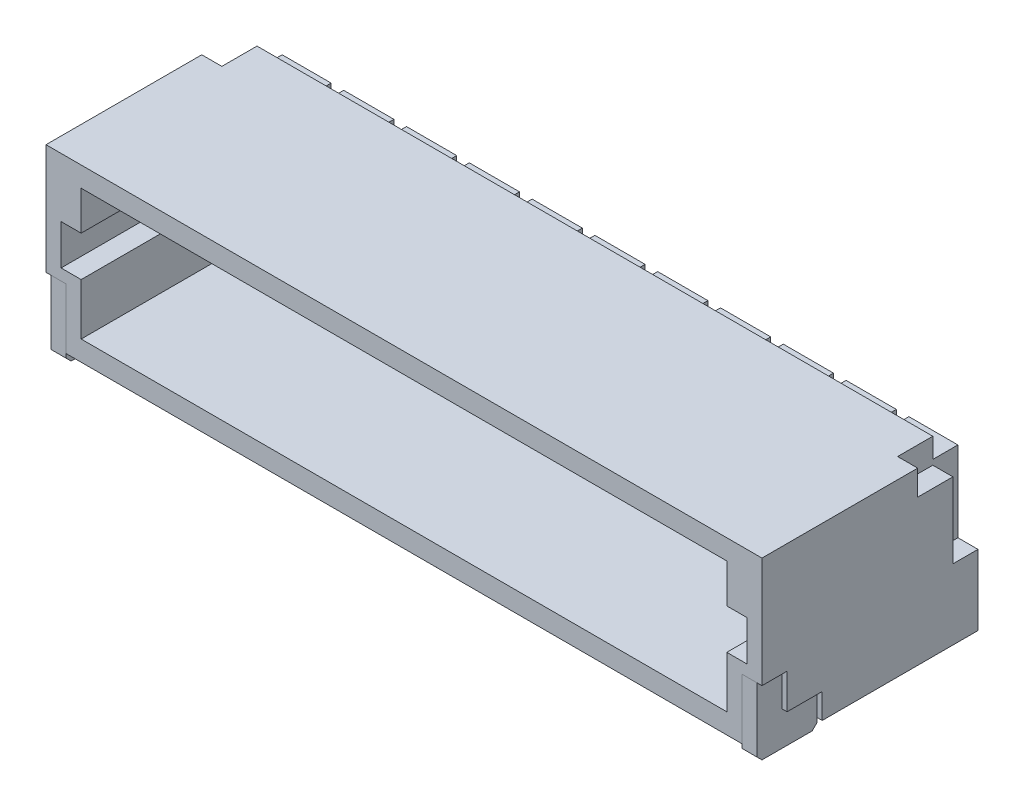
SolidWorks part; units mm, degrees
ref_plane "Front" through (0, 0, 0) normal (0, 0, 1) x (1, 0, 0)
ref_plane "Top" through (0, 0, 0) normal (0, 1, 0) x (1, 0, 0)
ref_plane "Right" through (0, 0, 0) normal (1, 0, 0) x (0, 0, -1)
sketch "Sketch1" plane through (0, 0, 0) normal (0, 0, 1) x (1, 0, 0)
  line L1 (4, -1.7) -> (-4, -1.7)
  line L2 (4, -1.7) -> (4, 1.7)
  line L3 (4, 1.7) -> (-4, 1.7)
  line L4 (-4, -1.7) -> (-4, 1.7)
  line L5 (4, -1.7) -> (-4, 1.7) construction
  line L6 (4, 1.7) -> (-4, -1.7) construction
  point P0 (0, 0)
  dimension "D1" = 3.4
  dimension "D2" = 8
extrude "Boss-Extrude1" add sketch "Sketch1" along normal mid plane 4.3
sketch "Sketch2" plane through (0, 0, 2.15) normal (0, 0, 1) x (1, 0, 0)
  line L0 (4, 1.7) -> (-4, 1.7) construction
  line L1 (3.3, -1.3) -> (-3.3, -1.3)
  line L2 (3.3, -1.3) -> (3.3, -0.275)
  line L3 (3.3, 1.3) -> (-3.3, 1.3)
  line L4 (-3.3, -1.3) -> (-3.3, -0.275)
  line L5 (3.3, -1.3) -> (-3.3, 1.3) construction
  line L6 (3.3, 1.3) -> (-3.3, -1.3) construction
  line L7 (-4, 1.7) -> (-4, -1.7) construction
  line L8 (-3.3, 0.525) -> (-3.3, 1.3)
  line L9 (-3.3, 0.525) -> (-3.7, 0.525)
  line L10 (-3.3, 0.525) -> (-3.3, -0.275) construction
  line L11 (-3.3, -0.275) -> (-3.7, -0.275)
  line L12 (-3.7, 0.525) -> (-3.7, -0.275)
  line L13 (3.3, 0.525) -> (3.7, 0.525)
  line L14 (3.3, 0.525) -> (3.3, -0.275) construction
  line L15 (3.3, -0.275) -> (3.7, -0.275)
  line L16 (3.7, 0.525) -> (3.7, -0.275)
  line L17 (-3.3, -0.275) -> (-3.3, 0.525) construction
  line L18 (3.3, 0.525) -> (3.3, 1.3)
  line L19 (3.3, -0.275) -> (3.3, 0.525) construction
  point P0 (0, 0)
  dimension "D1" = 0.4
  dimension "D2" = 0.7
  dimension "D3" = 0.4
  dimension "D4" = 0.8
  dimension "D5" = 1.175
extrude "Cut-Extrude1" cut sketch "Sketch2" against normal blind 3
sketch "Sketch5" plane through (-4, 0, 0) normal (-1, 0, 0) x (0, 0, 1)
  line L0 (2.15, -1.7) -> (2.15, -0.5)
  line L1 (2.15, 1.7) -> (2.15, -1.7) construction
  line L2 (2.15, -0.5) -> (1.65, -0.5)
  line L3 (1.65, -0.5) -> (1.65, -1.2)
  line L4 (1.65, -1.2) -> (0.95, -1.2)
  line L5 (0.95, -1.2) -> (0.95, -1.7)
  line L6 (2.15, -1.7) -> (-2.15, -1.7) construction
  line L7 (0.95, -1.7) -> (2.15, -1.7)
  line L14 (-1.65, 1.2) -> (-0.95, 1.2)
  line L15 (-0.95, 1.2) -> (-0.95, 1.7)
  line L16 (-0.95, 1.7) -> (-2.15, 1.7)
  line L17 (-2.15, 1.7) -> (-2.15, 0.5)
  line L18 (-2.15, 0.5) -> (-1.65, 0.5)
  line L19 (-1.65, 0.5) -> (-1.65, 1.2)
  line L20 (2.15, 1.7) -> (-2.15, 1.7) construction
  line L21 (-2.15, 1.7) -> (-2.15, -1.7) construction
  point P8 (0, 0)
  dimension "D1" = 1.2
  dimension "D2" = 0.5
  dimension "D3" = 2
extrude "Cut-Extrude2" cut sketch "Sketch5" against normal blind 0.4
mirror "Mirror1" about plane through (0, 0, 0) normal (1, 0, 0) of "Cut-Extrude2"
sketch "Sketch6" plane through (0, 0, -2.15) normal (0, 0, -1) x (-1, 0, 0)
  line L0 (-4, 1.7) -> (-4, -0.3)
  line L1 (-4, -1.7) -> (-4, 0.5) construction
  line L2 (-4, -0.3) -> (-3.6, -0.3)
  line L3 (-3.6, -0.3) -> (-3.6, 1.3)
  line L4 (-3.6, 1.7) -> (-3.6, 0.5) construction
  line L5 (-3.6, 1.3) -> (3.6, 1.3)
  line L6 (3.6, 1.2) -> (3.6, 1.7) construction
  line L7 (3.6, 1.3) -> (3.6, -0.3)
  line L8 (3.6, -0.3) -> (4, -0.3)
  line L9 (4, 0.5) -> (4, -1.7) construction
  line L10 (4, -0.3) -> (4, 1.7)
  line L11 (4, 1.7) -> (-4, 1.7)
  dimension "D1" = 0.4
  dimension "D2" = 2
extrude "Cut-Extrude3" cut sketch "Sketch6" against normal blind 0.5
sketch "Sketch7" plane through (0, 1.3, 0) normal (0, 1, 0) x (1, 0, 0)
  line L0 (3.6, 2.15) -> (-3.6, 2.15) construction
  line L1 (-0.125, 2.15) -> (0.125, 2.15)
  line L2 (-0.125, 2.15) -> (-0.125, 1.85)
  line L3 (-0.125, 1.85) -> (0.125, 1.85)
  line L4 (0.125, 2.15) -> (0.125, 1.85)
  line L5 (-1.125, 2.15) -> (-1.125, 1.85)
  line L6 (-1.375, 1.85) -> (-1.125, 1.85)
  line L7 (-1.375, 2.15) -> (-1.375, 1.85)
  line L8 (-1.375, 2.15) -> (-1.125, 2.15)
  line L9 (-2.375, 2.15) -> (-2.375, 1.85)
  line L10 (-2.625, 1.85) -> (-2.375, 1.85)
  line L11 (-2.625, 2.15) -> (-2.625, 1.85)
  line L12 (-2.625, 2.15) -> (-2.375, 2.15)
  line L13 (0.125, 2.15) -> (0.125, 1.85)
  line L14 (-0.125, 1.85) -> (0.125, 1.85)
  line L15 (-0.125, 2.15) -> (-0.125, 1.85)
  line L16 (-0.125, 2.15) -> (0.125, 2.15)
  line L17 (-1.125, 2.15) -> (-1.125, 1.85)
  line L18 (-1.375, 1.85) -> (-1.125, 1.85)
  line L19 (-1.375, 2.15) -> (-1.375, 1.85)
  line L20 (-1.375, 2.15) -> (-1.125, 2.15)
  line L21 (1.375, 2.15) -> (1.375, 1.85)
  line L22 (1.125, 1.85) -> (1.375, 1.85)
  line L23 (1.125, 2.15) -> (1.125, 1.85)
  line L24 (1.125, 2.15) -> (1.375, 2.15)
  line L25 (0.125, 2.15) -> (0.125, 1.85)
  line L26 (-0.125, 1.85) -> (0.125, 1.85)
  line L27 (-0.125, 2.15) -> (-0.125, 1.85)
  line L28 (-0.125, 2.15) -> (0.125, 2.15)
  line L29 (1.375, 2.15) -> (1.375, 1.85)
  line L30 (1.125, 1.85) -> (1.375, 1.85)
  line L31 (1.125, 2.15) -> (1.125, 1.85)
  line L32 (1.125, 2.15) -> (1.375, 2.15)
  line L33 (2.625, 2.15) -> (2.625, 1.85)
  line L34 (2.375, 1.85) -> (2.625, 1.85)
  line L35 (2.375, 2.15) -> (2.375, 1.85)
  line L36 (2.375, 2.15) -> (2.625, 2.15)
  point P6 (0, 1.85)
  line M7 (3.6, 2.15) -> (-3.6, 2.15)
  dimension "D1" = 0.25
  dimension "D2" = 0.3
  dimension "D5" = 1
  dimension "D3" = 3
  dimension "D4" = 3
extrude "Cut-Extrude4" cut sketch "Sketch7" against normal through all both and the other way through all contours L23 L22 L21 M7 | L7 L6 L5 M7 | L11 L10 L9 M7 | L4 L2 L3 M7 | L35 L34 L33 L36
sketch "Sketch8" plane through (0, 0, -0.85) normal (0, 0, 1) x (1, 0, 0)
  line L0 (0.125, 1.3) -> (-0.125, 1.3) construction
  line L1 (0.125, 1) -> (-0.125, 1)
  line L2 (1.375, 1) -> (1.375, 0.75)
  line L3 (-0.125, 1) -> (0.125, 1)
  line L4 (-0.125, 1) -> (-0.125, 0.75)
  line L5 (-0.125, 0.75) -> (0.125, 0.75)
  line L6 (0.125, 1) -> (0.125, 0.75)
  line L7 (1.125, 0.75) -> (1.375, 0.75)
  line L8 (1.125, 1) -> (1.125, 0.75)
  line L9 (1.375, 1) -> (1.125, 1)
  line L10 (2.625, 1) -> (2.625, 0.75)
  line L11 (2.375, 0.75) -> (2.625, 0.75)
  line L12 (2.375, 1) -> (2.375, 0.75)
  line L13 (2.625, 1) -> (2.375, 1)
  line L14 (0.125, 1) -> (0.125, 0.75)
  line L15 (-0.125, 0.75) -> (0.125, 0.75)
  line L16 (-0.125, 1) -> (-0.125, 0.75)
  line L17 (0.125, 1) -> (-0.125, 1)
  line L18 (1.375, 1) -> (1.375, 0.75)
  line L19 (1.125, 0.75) -> (1.375, 0.75)
  line L20 (1.125, 1) -> (1.125, 0.75)
  line L21 (1.375, 1) -> (1.125, 1)
  line L22 (-1.125, 1) -> (-1.125, 0.75)
  line L23 (-1.375, 0.75) -> (-1.125, 0.75)
  line L24 (-1.375, 1) -> (-1.375, 0.75)
  line L25 (-1.125, 1) -> (-1.375, 1)
  line L26 (0.125, 1) -> (0.125, 0.75)
  line L27 (-0.125, 0.75) -> (0.125, 0.75)
  line L28 (-0.125, 1) -> (-0.125, 0.75)
  line L29 (0.125, 1) -> (-0.125, 1)
  line L30 (-1.125, 1) -> (-1.125, 0.75)
  line L31 (-1.375, 0.75) -> (-1.125, 0.75)
  line L32 (-1.375, 1) -> (-1.375, 0.75)
  line L33 (-1.125, 1) -> (-1.375, 1)
  line L34 (-2.375, 1) -> (-2.375, 0.75)
  line L35 (-2.625, 0.75) -> (-2.375, 0.75)
  line L36 (-2.625, 1) -> (-2.625, 0.75)
  line L37 (-2.375, 1) -> (-2.625, 1)
  line L38 (3.3, 1.3) -> (-3.3, 1.3) construction
  line L39 (0.125, 1.3) -> (-0.125, 1.3) construction
  dimension "D3" = 1
  dimension "D4" = 0.3
  dimension "D5" = 0.25
  dimension "D1" = 3
  dimension "D2" = 3
extrude "Cut-Extrude5" cut sketch "Sketch8" against normal through all both and the other way through all contours L34 L37 L36 L35 | L22 L25 L24 L23 | L2 L9 L8 L7 | L6 L1 L4 L5 | L10 L13 L12 L11
sketch "Sketch9" plane through (0, 0, 0) normal (1, 0, 0) x (0, 0, -1)
  line L0 (1.85, -1.88) -> (2.95, -1.88)
  line L1 (2.95, -1.88) -> (2.95, -1.63)
  line L2 (2.95, -1.63) -> (2.15, -1.63)
  line L3 (2.15, -1.7) -> (2.15, -0.3) construction
  line L4 (2.15, -1.63) -> (2.15, 1)
  line L5 (2.15, 1.3) -> (2.15, -0.3) construction
  line L6 (2.15, 1) -> (-0.45, 1)
  line L7 (-0.45, 1) -> (-0.45, 0.75)
  line L8 (-0.45, 0.75) -> (1.85, 0.75)
  line L9 (1.85, -1.7) -> (1.85, 0.75) construction
  line L10 (1.85, 0.75) -> (1.85, -1.88)
  line L11 (1.85, 0.75) -> (0.85, 0.75) construction
  line L12 (1.85, 1) -> (0.85, 1) construction
  line L13 (-2.15, -0.5) -> (-2.15, 1.7) construction
  line L14 (-0.95, -1.7) -> (2.15, -1.7) construction
  dimension "D1" = 1.7
  dimension "D2" = 0.8
  dimension "D3" = 0.18
extrude "Boss-Extrude2" add sketch "Sketch9" along normal mid plane 0.25 separate body
chamfer "Chamfer2" distance 0.1 angle 45 1 edges at (0, -1.88, -1.85)
pattern_linear "LPattern1" count 3 spacing 1.25 along (1, 0, 0) count 3 spacing 1.25 along (-1, 0, 0) of bodies 108
sketch "Sketch10" plane through (3.6, 0, 0) normal (1, 0, 0) x (0, 0, -1)
  line L0 (-2.15, -0.5) -> (-2.15, -1.88)
  line L1 (-2.15, -1.88) -> (-0.95, -1.88)
  line L2 (-0.95, -1.88) -> (-0.95, -1.2)
  line L3 (-0.95, -1.2) -> (-1.65, -1.2)
  line L4 (-1.65, -0.5) -> (-1.65, -1.2) construction
  line L5 (-1.65, -1.2) -> (-1.65, -0.5)
  line L6 (-1.65, -0.5) -> (-2.15, -0.5)
  line L7 (-1.65, -1.2) -> (-0.95, -1.2) construction
  line L8 (-0.95, -1.2) -> (-0.95, -1.7) construction
  line L10 (-0.95, -1.7) -> (-2.15, -1.7) construction
  dimension "D1" = 0.18
extrude "Boss-Extrude3" add sketch "Sketch10" along normal blind 0.3 separate body
chamfer "Chamfer1" distance 0.1 angle 45 2 edges at (3.75, -1.88, 2.15) (3.75, -1.88, 0.95)
mirror "Mirror2" about plane through (0, 0, 0) normal (1, 0, 0) of bodies 117
sketch "Sketch11" plane through (0, 0, 2.15) normal (0, 0, 1) x (1, 0, 0)
  line L0 (4, 1.7) -> (-4, 1.7) construction
  line L1 (3.125, 1.7) -> (4, 1.7)
  line L2 (3.125, 1.7) -> (3.125, -1.88)
  line L3 (3.125, -1.88) -> (4, -1.88)
  line L4 (4, 1.7) -> (4, -1.88)
  line L5 (4, -0.5) -> (4, 1.7) construction
  line L6 (3.9, -1.88) -> (3.6, -1.88) construction
  line L8 (2.625, 1) -> (2.625, 0.75) construction
  dimension "D1" = 0.5
extrude "Cut-Extrude6" cut sketch "Sketch11" against normal through all both and the other way through all
mirror "Mirror3" about plane through (3.125, 1.7, -2.95) normal (-1, 0, 0) of bodies 108 119 118 112 111 110 109
combine bodies "Combine1" operation type add bodies to combine 121 119
